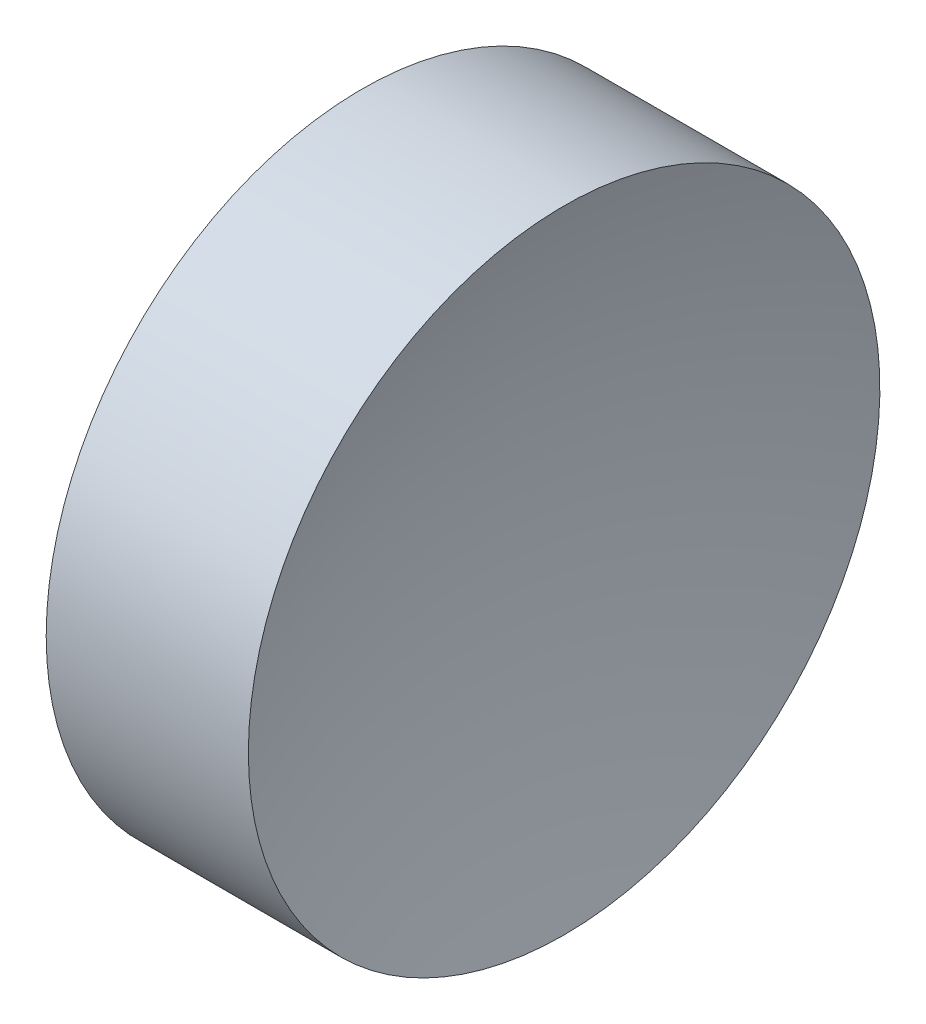
SolidWorks part; units mm, degrees
ref_plane "前视基准面" through (0, 0, 0) normal (0, 0, 1) x (1, 0, 0)
ref_plane "上视基准面" through (0, 0, 0) normal (0, 1, 0) x (1, 0, 0)
ref_plane "右视基准面" through (0, 0, 0) normal (1, 0, 0) x (0, 0, -1)
sketch "草图1" plane through (0, 0, 0) normal (0, 0, 1) x (1, 0, 0)
  line L0 (108.9851, 69.378) -> (132.7763, 69.378) construction
  line L1 (115.0927, 69.378) -> (115.0927, 81.878)
  line L2 (115.0927, 81.878) -> (123.0959, 81.878)
  line L3 (121.0927, 69.378) -> (115.0927, 69.378)
  arc A0 (123.0959, 81.878) -> (121.0927, 69.378) centre (161.0927, 69.378) ccw
  dimension "D1" = 8.0033
  dimension "D2" = 6
revolve "旋转1" add sketch "草图1" angle 360 about L0
